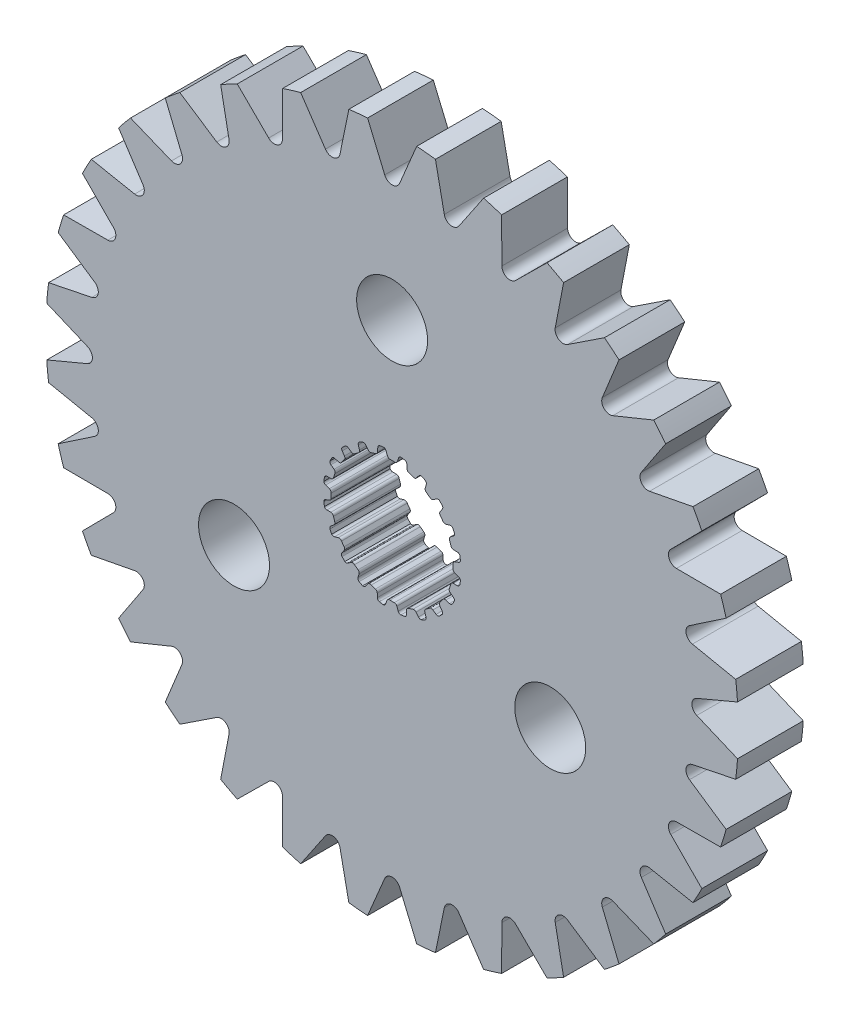
SolidWorks part; units mm, degrees
ref_plane "Front Plane" through (0, 0, 0) normal (0, 0, 1) x (1, 0, 0)
ref_plane "Top Plane" through (0, 0, 0) normal (0, 1, 0) x (1, 0, 0)
ref_plane "Right Plane" through (0, 0, 0) normal (1, 0, 0) x (0, 0, -1)
sketch "Sketch1" plane through (0, 0, 0) normal (0, 0, 1) x (1, 0, 0)
  line L0 (-0.1069, 2.9699) -> (0.1069, 2.9699)
  line L1 (0.3159, 3.2375) -> (0.2537, 3.0575)
  line L2 (-0.2964, 3.2367) -> (-0.2318, 3.0575)
  line L3 (-0.2964, 3.2367) -> (0.3159, 3.2375) construction
  line L4 (0, 3.3252) -> (0, 0) construction
  line L5 (-0.2318, 3.0575) -> (0.2537, 3.0575) construction
  line L6 (-0.4281, 3.3241) -> (0.4281, 3.3263) construction
  line L7 (0.7183, 3.1698) -> (0.7244, 2.9795)
  line L8 (0.816, 2.8576) -> (1.0195, 2.7915)
  line L9 (1.3009, 2.9815) -> (1.1862, 2.8295)
  line L10 (1.6627, 2.7927) -> (1.6097, 2.6099)
  line L11 (1.6591, 2.4655) -> (1.8322, 2.3398)
  line L12 (2.1585, 2.4335) -> (2.0025, 2.3245)
  line L13 (2.4443, 2.1423) -> (2.3374, 1.9847)
  line L14 (2.3398, 1.8322) -> (2.4655, 1.6591)
  line L15 (2.8049, 1.6474) -> (2.6228, 1.5919)
  line L16 (2.9866, 1.2821) -> (2.8363, 1.1653)
  line L17 (2.7915, 1.0195) -> (2.8576, 0.816)
  line L18 (3.1767, 0.7) -> (2.9863, 0.7035)
  line L19 (3.2367, 0.2964) -> (3.0575, 0.2318)
  line L20 (2.9699, 0.1069) -> (2.9699, -0.1069)
  line L21 (3.2375, -0.3159) -> (3.0575, -0.2537)
  line L22 (3.1698, -0.7183) -> (2.9795, -0.7244)
  line L23 (2.8576, -0.816) -> (2.7915, -1.0195)
  line L24 (2.9815, -1.3009) -> (2.8295, -1.1862)
  line L25 (2.7927, -1.6627) -> (2.6099, -1.6097)
  line L26 (2.4655, -1.6591) -> (2.3398, -1.8322)
  line L27 (2.4335, -2.1585) -> (2.3245, -2.0025)
  line L28 (2.1423, -2.4443) -> (1.9847, -2.3374)
  line L29 (1.8322, -2.3398) -> (1.6591, -2.4655)
  line L30 (1.6474, -2.8049) -> (1.5919, -2.6228)
  line L31 (1.2821, -2.9866) -> (1.1653, -2.8363)
  line L32 (1.0195, -2.7915) -> (0.816, -2.8576)
  line L33 (0.7, -3.1767) -> (0.7035, -2.9863)
  line L34 (0.2964, -3.2367) -> (0.2318, -3.0575)
  line L35 (0.1069, -2.9699) -> (-0.1069, -2.9699)
  line L36 (-0.3159, -3.2375) -> (-0.2537, -3.0575)
  line L37 (-0.7183, -3.1698) -> (-0.7244, -2.9795)
  line L38 (-0.816, -2.8576) -> (-1.0195, -2.7915)
  line L39 (-1.3009, -2.9815) -> (-1.1862, -2.8295)
  line L40 (-1.6627, -2.7927) -> (-1.6097, -2.6099)
  line L41 (-1.6591, -2.4655) -> (-1.8322, -2.3398)
  line L42 (-2.1585, -2.4335) -> (-2.0025, -2.3245)
  line L43 (-2.4443, -2.1423) -> (-2.3374, -1.9847)
  line L44 (-2.3398, -1.8322) -> (-2.4655, -1.6591)
  line L45 (-2.8049, -1.6474) -> (-2.6228, -1.5919)
  line L46 (-2.9866, -1.2821) -> (-2.8363, -1.1653)
  line L47 (-2.7915, -1.0195) -> (-2.8576, -0.816)
  line L48 (-3.1767, -0.7) -> (-2.9863, -0.7035)
  line L49 (-3.2367, -0.2964) -> (-3.0575, -0.2318)
  line L50 (-2.9699, -0.1069) -> (-2.9699, 0.1069)
  line L51 (-3.2375, 0.3159) -> (-3.0575, 0.2537)
  line L52 (-3.1698, 0.7183) -> (-2.9795, 0.7244)
  line L53 (-2.8576, 0.816) -> (-2.7915, 1.0195)
  line L54 (-2.9815, 1.3009) -> (-2.8295, 1.1862)
  line L55 (-2.7927, 1.6627) -> (-2.6099, 1.6097)
  line L56 (-2.4655, 1.6591) -> (-2.3398, 1.8322)
  line L57 (-2.4335, 2.1585) -> (-2.3245, 2.0025)
  line L58 (-2.1423, 2.4443) -> (-1.9847, 2.3374)
  line L59 (-1.8322, 2.3398) -> (-1.6591, 2.4655)
  line L60 (-1.6474, 2.8049) -> (-1.5919, 2.6228)
  line L61 (-1.2821, 2.9866) -> (-1.1653, 2.8363)
  line L62 (-1.0195, 2.7915) -> (-0.816, 2.8576)
  line L63 (-0.7, 3.1767) -> (-0.7035, 2.9863)
  line L64 (0.4281, 3.3263) -> (0.62, 3.2938)
  line L65 (1.4351, 3.0312) -> (1.6075, 2.9409)
  line L66 (2.3015, 2.4394) -> (2.4376, 2.3003)
  line L67 (2.9427, 1.6088) -> (3.0291, 1.4344)
  line L68 (3.2958, 0.6207) -> (3.3241, 0.4281)
  line L69 (3.3263, -0.4281) -> (3.2938, -0.62)
  line L70 (3.0312, -1.4351) -> (2.9409, -1.6075)
  line L71 (2.4394, -2.3015) -> (2.3003, -2.4376)
  line L72 (1.6088, -2.9427) -> (1.4344, -3.0291)
  line L73 (0.6207, -3.2958) -> (0.4281, -3.3241)
  line L74 (-0.4281, -3.3263) -> (-0.62, -3.2938)
  line L75 (-1.4351, -3.0312) -> (-1.6075, -2.9409)
  line L76 (-2.3015, -2.4394) -> (-2.4376, -2.3003)
  line L77 (-2.9427, -1.6088) -> (-3.0291, -1.4344)
  line L78 (-3.2958, -0.6207) -> (-3.3241, -0.4281)
  line L79 (-3.3263, 0.4281) -> (-3.2938, 0.62)
  line L80 (-3.0312, 1.4351) -> (-2.9409, 1.6075)
  line L81 (-2.4394, 2.3015) -> (-2.3003, 2.4376)
  line L82 (-1.6088, 2.9427) -> (-1.4344, 3.0291)
  line L83 (-0.6207, 3.2958) -> (-0.4281, 3.3241)
  arc A0 (0.2537, 3.0575) -> (0.1069, 2.9699) centre (0.1283, 3.1009) cw
  arc A1 (-0.2318, 3.0575) -> (-0.1069, 2.9699) centre (-0.1069, 3.1026) ccw
  arc A2 (0.62, 3.2938) -> (0.7183, 3.1698) centre (0.5856, 3.1656) cw
  arc A3 (0.7244, 2.9795) -> (0.816, 2.8576) centre (0.857, 2.9838) ccw
  arc A4 (-0.4281, 3.3241) -> (-0.2964, 3.2367) centre (-0.4213, 3.1916) cw
  arc A5 (0.4281, 3.3263) -> (0.3159, 3.2375) centre (0.4413, 3.1942) ccw
  arc A6 (1.1862, 2.8295) -> (1.0195, 2.7915) centre (1.0802, 2.9095) cw
  arc A7 (1.4351, 3.0312) -> (1.3009, 2.9815) centre (1.4068, 2.9015) ccw
  arc A8 (1.6075, 2.9409) -> (1.6627, 2.7927) centre (1.5352, 2.8297) cw
  arc A9 (1.6097, 2.6099) -> (1.6591, 2.4655) centre (1.7371, 2.5729) ccw
  arc A10 (2.0025, 2.3245) -> (1.8322, 2.3398) centre (1.9264, 2.4332) cw
  arc A11 (2.3015, 2.4394) -> (2.1585, 2.4335) centre (2.2346, 2.3248) ccw
  arc A12 (2.4376, 2.3003) -> (2.4443, 2.1423) centre (2.3345, 2.2168) cw
  arc A13 (2.3374, 1.9847) -> (2.3398, 1.8322) centre (2.4472, 1.9102) ccw
  arc A14 (2.6228, 1.5919) -> (2.4655, 1.6591) centre (2.5841, 1.7189) cw
  arc A15 (2.9427, 1.6088) -> (2.8049, 1.6474) centre (2.8436, 1.5205) ccw
  arc A16 (3.0291, 1.4344) -> (2.9866, 1.2821) centre (2.9052, 1.3869) cw
  arc A17 (2.8363, 1.1653) -> (2.7915, 1.0195) centre (2.9177, 1.0605) ccw
  arc A18 (2.9863, 0.7035) -> (2.8576, 0.816) centre (2.9887, 0.8362) cw
  arc A19 (3.2958, 0.6207) -> (3.1767, 0.7) centre (3.1743, 0.5673) ccw
  arc A20 (3.3241, 0.4281) -> (3.2367, 0.2964) centre (3.1916, 0.4213) cw
  arc A21 (3.0575, 0.2318) -> (2.9699, 0.1069) centre (3.1026, 0.1069) ccw
  arc A22 (3.0575, -0.2537) -> (2.9699, -0.1069) centre (3.1009, -0.1283) cw
  arc A23 (3.3263, -0.4281) -> (3.2375, -0.3159) centre (3.1942, -0.4413) ccw
  arc A24 (3.2938, -0.62) -> (3.1698, -0.7183) centre (3.1656, -0.5856) cw
  arc A25 (2.9795, -0.7244) -> (2.8576, -0.816) centre (2.9838, -0.857) ccw
  arc A26 (2.8295, -1.1862) -> (2.7915, -1.0195) centre (2.9095, -1.0802) cw
  arc A27 (3.0312, -1.4351) -> (2.9815, -1.3009) centre (2.9015, -1.4068) ccw
  arc A28 (2.9409, -1.6075) -> (2.7927, -1.6627) centre (2.8297, -1.5352) cw
  arc A29 (2.6099, -1.6097) -> (2.4655, -1.6591) centre (2.5729, -1.7371) ccw
  arc A30 (2.3245, -2.0025) -> (2.3398, -1.8322) centre (2.4332, -1.9264) cw
  arc A31 (2.4394, -2.3015) -> (2.4335, -2.1585) centre (2.3248, -2.2346) ccw
  arc A32 (2.3003, -2.4376) -> (2.1423, -2.4443) centre (2.2168, -2.3345) cw
  arc A33 (1.9847, -2.3374) -> (1.8322, -2.3398) centre (1.9102, -2.4472) ccw
  arc A34 (1.5919, -2.6228) -> (1.6591, -2.4655) centre (1.7189, -2.5841) cw
  arc A35 (1.6088, -2.9427) -> (1.6474, -2.8049) centre (1.5205, -2.8436) ccw
  arc A36 (1.4344, -3.0291) -> (1.2821, -2.9866) centre (1.3869, -2.9052) cw
  arc A37 (1.1653, -2.8363) -> (1.0195, -2.7915) centre (1.0605, -2.9177) ccw
  arc A38 (0.7035, -2.9863) -> (0.816, -2.8576) centre (0.8362, -2.9887) cw
  arc A39 (0.6207, -3.2958) -> (0.7, -3.1767) centre (0.5673, -3.1743) ccw
  arc A40 (0.4281, -3.3241) -> (0.2964, -3.2367) centre (0.4213, -3.1916) cw
  arc A41 (0.2318, -3.0575) -> (0.1069, -2.9699) centre (0.1069, -3.1026) ccw
  arc A42 (-0.2537, -3.0575) -> (-0.1069, -2.9699) centre (-0.1283, -3.1009) cw
  arc A43 (-0.4281, -3.3263) -> (-0.3159, -3.2375) centre (-0.4413, -3.1942) ccw
  arc A44 (-0.62, -3.2938) -> (-0.7183, -3.1698) centre (-0.5856, -3.1656) cw
  arc A45 (-0.7244, -2.9795) -> (-0.816, -2.8576) centre (-0.857, -2.9838) ccw
  arc A46 (-1.1862, -2.8295) -> (-1.0195, -2.7915) centre (-1.0802, -2.9095) cw
  arc A47 (-1.4351, -3.0312) -> (-1.3009, -2.9815) centre (-1.4068, -2.9015) ccw
  arc A48 (-1.6075, -2.9409) -> (-1.6627, -2.7927) centre (-1.5352, -2.8297) cw
  arc A49 (-1.6097, -2.6099) -> (-1.6591, -2.4655) centre (-1.7371, -2.5729) ccw
  arc A50 (-2.0025, -2.3245) -> (-1.8322, -2.3398) centre (-1.9264, -2.4332) cw
  arc A51 (-2.3015, -2.4394) -> (-2.1585, -2.4335) centre (-2.2346, -2.3248) ccw
  arc A52 (-2.4376, -2.3003) -> (-2.4443, -2.1423) centre (-2.3345, -2.2168) cw
  arc A53 (-2.3374, -1.9847) -> (-2.3398, -1.8322) centre (-2.4472, -1.9102) ccw
  arc A54 (-2.6228, -1.5919) -> (-2.4655, -1.6591) centre (-2.5841, -1.7189) cw
  arc A55 (-2.9427, -1.6088) -> (-2.8049, -1.6474) centre (-2.8436, -1.5205) ccw
  arc A56 (-3.0291, -1.4344) -> (-2.9866, -1.2821) centre (-2.9052, -1.3869) cw
  arc A57 (-2.8363, -1.1653) -> (-2.7915, -1.0195) centre (-2.9177, -1.0605) ccw
  arc A58 (-2.9863, -0.7035) -> (-2.8576, -0.816) centre (-2.9887, -0.8362) cw
  arc A59 (-3.2958, -0.6207) -> (-3.1767, -0.7) centre (-3.1743, -0.5673) ccw
  arc A60 (-3.3241, -0.4281) -> (-3.2367, -0.2964) centre (-3.1916, -0.4213) cw
  arc A61 (-3.0575, -0.2318) -> (-2.9699, -0.1069) centre (-3.1026, -0.1069) ccw
  arc A62 (-3.0575, 0.2537) -> (-2.9699, 0.1069) centre (-3.1009, 0.1283) cw
  arc A63 (-3.3263, 0.4281) -> (-3.2375, 0.3159) centre (-3.1942, 0.4413) ccw
  arc A64 (-3.2938, 0.62) -> (-3.1698, 0.7183) centre (-3.1656, 0.5856) cw
  arc A65 (-2.9795, 0.7244) -> (-2.8576, 0.816) centre (-2.9838, 0.857) ccw
  arc A66 (-2.8295, 1.1862) -> (-2.7915, 1.0195) centre (-2.9095, 1.0802) cw
  arc A67 (-3.0312, 1.4351) -> (-2.9815, 1.3009) centre (-2.9015, 1.4068) ccw
  arc A68 (-2.9409, 1.6075) -> (-2.7927, 1.6627) centre (-2.8297, 1.5352) cw
  arc A69 (-2.6099, 1.6097) -> (-2.4655, 1.6591) centre (-2.5729, 1.7371) ccw
  arc A70 (-2.3245, 2.0025) -> (-2.3398, 1.8322) centre (-2.4332, 1.9264) cw
  arc A71 (-2.4394, 2.3015) -> (-2.4335, 2.1585) centre (-2.3248, 2.2346) ccw
  arc A72 (-2.3003, 2.4376) -> (-2.1423, 2.4443) centre (-2.2168, 2.3345) cw
  arc A73 (-1.9847, 2.3374) -> (-1.8322, 2.3398) centre (-1.9102, 2.4472) ccw
  arc A74 (-1.5919, 2.6228) -> (-1.6591, 2.4655) centre (-1.7189, 2.5841) cw
  arc A75 (-1.6088, 2.9427) -> (-1.6474, 2.8049) centre (-1.5205, 2.8436) ccw
  arc A76 (-1.4344, 3.0291) -> (-1.2821, 2.9866) centre (-1.3869, 2.9052) cw
  arc A77 (-1.1653, 2.8363) -> (-1.0195, 2.7915) centre (-1.0605, 2.9177) ccw
  arc A78 (-0.7035, 2.9863) -> (-0.816, 2.8576) centre (-0.8362, 2.9887) cw
  arc A79 (-0.6207, 3.2958) -> (-0.7, 3.1767) centre (-0.5673, 3.1743) ccw
  circle A80 centre (0, 0) radius 16.8606
  point P14 (0, 2.9699)
  point P247 (0, 0)
  dimension "D4" = 0.1327
  dimension "D8" = 20
  dimension "D9" = 33.7212
  dimension "D1" = 2.9699
  dimension "D2" = 0.2139
  dimension "D3" = 0.1904
  dimension "D5" = 0.0877
  dimension "D6" = 0.4855
  dimension "D7" = 0.8563
extrude "Boss-Extrude1" add sketch "Sketch1" along normal blind 3.2004
sketch "Sketch2" plane through (0, 0, 3.2004) normal (0, 0, 1) x (1, 0, 0)
  line L0 (0, 16.8181) -> (0, 0) construction
  line L1 (1.557, 31.6527) -> (0, 0) construction
  line L2 (-1.1958, 16.8181) -> (1.1958, 16.8181) construction
  line L3 (-0.7785, 15.8263) -> (0.7785, 15.8263) construction
  line L4 (-1.1958, 16.8181) -> (-0.3613, 14.8345)
  line L5 (1.1958, 16.8181) -> (0.3613, 14.8345)
  line L6 (4.4538, 16.2617) -> (3.2484, 14.479)
  line L7 (2.1083, 16.7283) -> (2.5398, 14.62)
  line L8 (7.5408, 15.0803) -> (6.0107, 13.5671)
  line L9 (5.3313, 15.9955) -> (5.3432, 13.8436)
  line L10 (10.3379, 13.3195) -> (8.542, 12.1338)
  line L11 (8.3494, 14.6481) -> (7.9413, 12.5352)
  line L12 (12.7378, 11.0467) -> (10.7451, 10.2342)
  line L13 (11.0467, 12.7378) -> (10.2342, 10.7451)
  line L14 (14.6481, 8.3494) -> (12.5352, 7.9413)
  line L15 (13.3195, 10.3379) -> (12.1338, 8.542)
  line L16 (15.9955, 5.3313) -> (13.8436, 5.3432)
  line L17 (15.0803, 7.5408) -> (13.5671, 6.0107)
  line L18 (16.7283, 2.1083) -> (14.62, 2.5398)
  line L19 (16.2617, 4.4538) -> (14.479, 3.2484)
  line L20 (16.8181, -1.1958) -> (14.8345, -0.3613)
  line L21 (16.8181, 1.1958) -> (14.8345, 0.3613)
  line L22 (16.2617, -4.4538) -> (14.479, -3.2484)
  line L23 (16.7283, -2.1083) -> (14.62, -2.5398)
  line L24 (15.0803, -7.5408) -> (13.5671, -6.0107)
  line L25 (15.9955, -5.3313) -> (13.8436, -5.3432)
  line L26 (13.3195, -10.3379) -> (12.1338, -8.542)
  line L27 (14.6481, -8.3494) -> (12.5352, -7.9413)
  line L28 (11.0467, -12.7378) -> (10.2342, -10.7451)
  line L29 (12.7378, -11.0467) -> (10.7451, -10.2342)
  line L30 (8.3494, -14.6481) -> (7.9413, -12.5352)
  line L31 (10.3379, -13.3195) -> (8.542, -12.1338)
  line L32 (5.3313, -15.9955) -> (5.3432, -13.8436)
  line L33 (7.5408, -15.0803) -> (6.0107, -13.5671)
  line L34 (2.1083, -16.7283) -> (2.5398, -14.62)
  line L35 (4.4538, -16.2617) -> (3.2484, -14.479)
  line L36 (-1.1958, -16.8181) -> (-0.3613, -14.8345)
  line L37 (1.1958, -16.8181) -> (0.3613, -14.8345)
  line L38 (-4.4538, -16.2617) -> (-3.2484, -14.479)
  line L39 (-2.1083, -16.7283) -> (-2.5398, -14.62)
  line L40 (-7.5408, -15.0803) -> (-6.0107, -13.5671)
  line L41 (-5.3313, -15.9955) -> (-5.3432, -13.8436)
  line L42 (-10.3379, -13.3195) -> (-8.542, -12.1338)
  line L43 (-8.3494, -14.6481) -> (-7.9413, -12.5352)
  line L44 (-12.7378, -11.0467) -> (-10.7451, -10.2342)
  line L45 (-11.0467, -12.7378) -> (-10.2342, -10.7451)
  line L46 (-14.6481, -8.3494) -> (-12.5352, -7.9413)
  line L47 (-13.3195, -10.3379) -> (-12.1338, -8.542)
  line L48 (-15.9955, -5.3313) -> (-13.8436, -5.3432)
  line L49 (-15.0803, -7.5408) -> (-13.5671, -6.0107)
  line L50 (-16.7283, -2.1083) -> (-14.62, -2.5398)
  line L51 (-16.2617, -4.4538) -> (-14.479, -3.2484)
  line L52 (-16.8181, 1.1958) -> (-14.8345, 0.3613)
  line L53 (-16.8181, -1.1958) -> (-14.8345, -0.3613)
  line L54 (-16.2617, 4.4538) -> (-14.479, 3.2484)
  line L55 (-16.7283, 2.1083) -> (-14.62, 2.5398)
  line L56 (-15.0803, 7.5408) -> (-13.5671, 6.0107)
  line L57 (-15.9955, 5.3313) -> (-13.8436, 5.3432)
  line L58 (-13.3195, 10.3379) -> (-12.1338, 8.542)
  line L59 (-14.6481, 8.3494) -> (-12.5352, 7.9413)
  line L60 (-11.0467, 12.7378) -> (-10.2342, 10.7451)
  line L61 (-12.7378, 11.0467) -> (-10.7451, 10.2342)
  line L62 (-8.3494, 14.6481) -> (-7.9413, 12.5352)
  line L63 (-10.3379, 13.3195) -> (-8.542, 12.1338)
  line L64 (-5.3313, 15.9955) -> (-5.3432, 13.8436)
  line L65 (-7.5408, 15.0803) -> (-6.0107, 13.5671)
  line L66 (-2.1083, 16.7283) -> (-2.5398, 14.62)
  line L67 (-4.4538, 16.2617) -> (-3.2484, 14.479)
  circle A0 centre (0, 0) radius 16.8606 construction
  arc A1 (-0.3613, 14.8345) -> (0.3613, 14.8345) centre (0, 14.9865) ccw
  arc A2 (-1.1958, 16.8181) -> (1.1958, 16.8181) centre (0, 0) cw
  arc A3 (2.1083, 16.7283) -> (4.4538, 16.2617) centre (0, 0) cw
  arc A4 (2.5398, 14.62) -> (3.2484, 14.479) centre (2.9237, 14.6986) ccw
  arc A5 (5.3313, 15.9955) -> (7.5408, 15.0803) centre (0, 0) cw
  arc A6 (5.3432, 13.8436) -> (6.0107, 13.5671) centre (5.7351, 13.8457) ccw
  arc A7 (8.3494, 14.6481) -> (10.3379, 13.3195) centre (0, 0) cw
  arc A8 (7.9413, 12.5352) -> (8.542, 12.1338) centre (8.3261, 12.4608) ccw
  arc A9 (11.0467, 12.7378) -> (12.7378, 11.0467) centre (0, 0) cw
  arc A10 (10.2342, 10.7451) -> (10.7451, 10.2342) centre (10.5971, 10.5971) ccw
  arc A11 (13.3195, 10.3379) -> (14.6481, 8.3494) centre (0, 0) cw
  arc A12 (12.1338, 8.542) -> (12.5352, 7.9413) centre (12.4608, 8.3261) ccw
  arc A13 (15.0803, 7.5408) -> (15.9955, 5.3313) centre (0, 0) cw
  arc A14 (13.5671, 6.0107) -> (13.8436, 5.3432) centre (13.8457, 5.7351) ccw
  arc A15 (16.2617, 4.4538) -> (16.7283, 2.1083) centre (0, 0) cw
  arc A16 (14.479, 3.2484) -> (14.62, 2.5398) centre (14.6986, 2.9237) ccw
  arc A17 (16.8181, 1.1958) -> (16.8181, -1.1958) centre (0, 0) cw
  arc A18 (14.8345, 0.3613) -> (14.8345, -0.3613) centre (14.9865, 0) ccw
  arc A19 (16.7283, -2.1083) -> (16.2617, -4.4538) centre (0, 0) cw
  arc A20 (14.62, -2.5398) -> (14.479, -3.2484) centre (14.6986, -2.9237) ccw
  arc A21 (15.9955, -5.3313) -> (15.0803, -7.5408) centre (0, 0) cw
  arc A22 (13.8436, -5.3432) -> (13.5671, -6.0107) centre (13.8457, -5.7351) ccw
  arc A23 (14.6481, -8.3494) -> (13.3195, -10.3379) centre (0, 0) cw
  arc A24 (12.5352, -7.9413) -> (12.1338, -8.542) centre (12.4608, -8.3261) ccw
  arc A25 (12.7378, -11.0467) -> (11.0467, -12.7378) centre (0, 0) cw
  arc A26 (10.7451, -10.2342) -> (10.2342, -10.7451) centre (10.5971, -10.5971) ccw
  arc A27 (10.3379, -13.3195) -> (8.3494, -14.6481) centre (0, 0) cw
  arc A28 (8.542, -12.1338) -> (7.9413, -12.5352) centre (8.3261, -12.4608) ccw
  arc A29 (7.5408, -15.0803) -> (5.3313, -15.9955) centre (0, 0) cw
  arc A30 (6.0107, -13.5671) -> (5.3432, -13.8436) centre (5.7351, -13.8457) ccw
  arc A31 (4.4538, -16.2617) -> (2.1083, -16.7283) centre (0, 0) cw
  arc A32 (3.2484, -14.479) -> (2.5398, -14.62) centre (2.9237, -14.6986) ccw
  arc A33 (1.1958, -16.8181) -> (-1.1958, -16.8181) centre (0, 0) cw
  arc A34 (0.3613, -14.8345) -> (-0.3613, -14.8345) centre (0, -14.9865) ccw
  arc A35 (-2.1083, -16.7283) -> (-4.4538, -16.2617) centre (0, 0) cw
  arc A36 (-2.5398, -14.62) -> (-3.2484, -14.479) centre (-2.9237, -14.6986) ccw
  arc A37 (-5.3313, -15.9955) -> (-7.5408, -15.0803) centre (0, 0) cw
  arc A38 (-5.3432, -13.8436) -> (-6.0107, -13.5671) centre (-5.7351, -13.8457) ccw
  arc A39 (-8.3494, -14.6481) -> (-10.3379, -13.3195) centre (0, 0) cw
  arc A40 (-7.9413, -12.5352) -> (-8.542, -12.1338) centre (-8.3261, -12.4608) ccw
  arc A41 (-11.0467, -12.7378) -> (-12.7378, -11.0467) centre (0, 0) cw
  arc A42 (-10.2342, -10.7451) -> (-10.7451, -10.2342) centre (-10.5971, -10.5971) ccw
  arc A43 (-13.3195, -10.3379) -> (-14.6481, -8.3494) centre (0, 0) cw
  arc A44 (-12.1338, -8.542) -> (-12.5352, -7.9413) centre (-12.4608, -8.3261) ccw
  arc A45 (-15.0803, -7.5408) -> (-15.9955, -5.3313) centre (0, 0) cw
  arc A46 (-13.5671, -6.0107) -> (-13.8436, -5.3432) centre (-13.8457, -5.7351) ccw
  arc A47 (-16.2617, -4.4538) -> (-16.7283, -2.1083) centre (0, 0) cw
  arc A48 (-14.479, -3.2484) -> (-14.62, -2.5398) centre (-14.6986, -2.9237) ccw
  arc A49 (-16.8181, -1.1958) -> (-16.8181, 1.1958) centre (0, 0) cw
  arc A50 (-14.8345, -0.3613) -> (-14.8345, 0.3613) centre (-14.9865, 0) ccw
  arc A51 (-16.7283, 2.1083) -> (-16.2617, 4.4538) centre (0, 0) cw
  arc A52 (-14.62, 2.5398) -> (-14.479, 3.2484) centre (-14.6986, 2.9237) ccw
  arc A53 (-15.9955, 5.3313) -> (-15.0803, 7.5408) centre (0, 0) cw
  arc A54 (-13.8436, 5.3432) -> (-13.5671, 6.0107) centre (-13.8457, 5.7351) ccw
  arc A55 (-14.6481, 8.3494) -> (-13.3195, 10.3379) centre (0, 0) cw
  arc A56 (-12.5352, 7.9413) -> (-12.1338, 8.542) centre (-12.4608, 8.3261) ccw
  arc A57 (-12.7378, 11.0467) -> (-11.0467, 12.7378) centre (0, 0) cw
  arc A58 (-10.7451, 10.2342) -> (-10.2342, 10.7451) centre (-10.5971, 10.5971) ccw
  arc A59 (-10.3379, 13.3195) -> (-8.3494, 14.6481) centre (0, 0) cw
  arc A60 (-8.542, 12.1338) -> (-7.9413, 12.5352) centre (-8.3261, 12.4608) ccw
  arc A61 (-7.5408, 15.0803) -> (-5.3313, 15.9955) centre (0, 0) cw
  arc A62 (-6.0107, 13.5671) -> (-5.3432, 13.8436) centre (-5.7351, 13.8457) ccw
  arc A63 (-4.4538, 16.2617) -> (-2.1083, 16.7283) centre (0, 0) cw
  arc A64 (-3.2484, 14.479) -> (-2.5398, 14.62) centre (-2.9237, 14.6986) ccw
  point P9 (0, 15.8263)
  point P171 (0, 0)
  dimension "D1" = 0.9918
  dimension "D2" = 1.557
  dimension "D3" = 20
  dimension "D4" = 32
extrude "Cut-Extrude1" cut sketch "Sketch2" against normal up to surface (3.2004 mm away) up to face at (16.8606, 0, 0)
sketch "Sketch5" plane through (0, 0, 3.2004) normal (0, 0, 1) x (1, 0, 0)
  line L0 (0, 8.89) -> (0, 0) construction
  line L1 (0, 3.3252) -> (0, 0) construction
  circle A0 centre (0, 0) radius 16.8606 construction
  circle A1 centre (0, 8.89) radius 1.7272
  circle A2 centre (7.699, -4.445) radius 1.7272
  circle A3 centre (-7.699, -4.445) radius 1.7272
  point P15 (0, 0)
  dimension "D2" = 3.4544
  dimension "D1" = 8.89
  dimension "D3" = 3
extrude "Cut-Extrude2" cut sketch "Sketch5" against normal up to surface (3.2004 mm away) up to face at (0, 0, 0)
sketch "Sketch3" plane through (0, 0, 3.2004) normal (0, 0, 1) x (1, 0, 0)
  circle A0 centre (0, 0) radius 15.8688 construction
  circle A1 centre (0, 0) radius 16.8606 construction
  dimension "D1" = 31.7376
